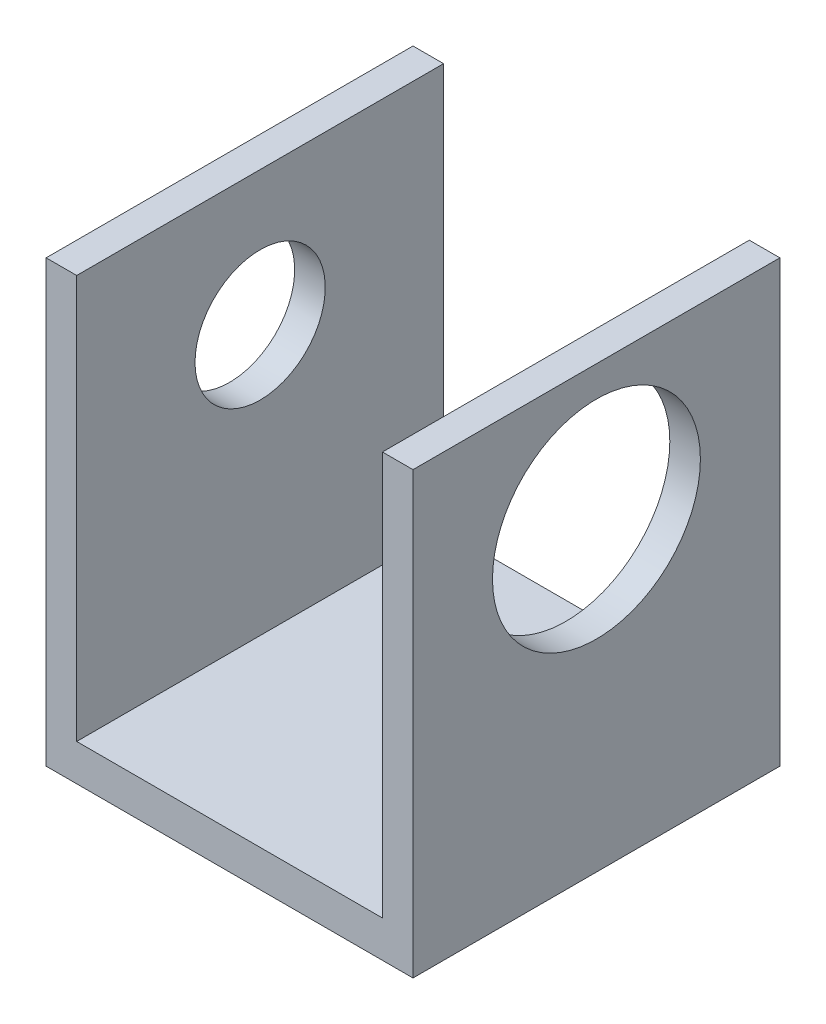
SolidWorks part; units mm, degrees
ref_plane "Front Plane" through (0, 0, 0) normal (0, 0, 1) x (1, 0, 0)
ref_plane "Top Plane" through (0, 0, 0) normal (0, 1, 0) x (1, 0, 0)
ref_plane "Right Plane" through (0, 0, 0) normal (1, 0, 0) x (0, 0, -1)
sketch "Sketch1" plane through (0, 0, 0) normal (0, 0, 1) x (1, 0, 0)
  line L0 (-3.3539, 6.8522) -> (-3.3539, -2.2918)
  line L1 (-3.3539, -2.2918) -> (4.2661, -2.2918)
  line L2 (4.2661, -2.2918) -> (4.2661, 6.8522)
  line L3 (3.6311, 6.8522) -> (3.6311, -1.5298)
  line L4 (3.6311, -1.5298) -> (-2.7189, -1.5298)
  line L5 (-2.7189, -1.5298) -> (-2.7189, 6.8522)
  line L6 (-2.7189, 6.8522) -> (-3.3539, 6.8522)
  line L7 (3.6311, 6.8522) -> (4.2661, 6.8522)
  dimension "D1" = 6.35
  dimension "D2" = 7.62
  dimension "D3" = 0.635
  dimension "D4" = 8.382
  dimension "D5" = 9.144
  dimension "D6" = 8.382
extrude "Boss-Extrude1" add sketch "Sketch1" along normal blind 7.62
sketch "Sketch2" plane through (-3.3539, 0, 0) normal (-1, 0, 0) x (0, 0, 1)
  line L0 (7.62, 6.8522) -> (0, 6.8522) construction
  line L1 (3.81, -2.2918) -> (3.81, 6.8522) construction
  point P0 (3.81, 4.0582)
  dimension "D1" = 2.794
hole_wizard "#6-32 Tapped Hole1" positions "Sketch3" profile "Sketch4" tap size "#6-32" standard "ANSI Inch" end condition up to next
sketch "Sketch3" plane through (-3.3539, 0, 0) normal (-1, 0, 0) x (0, 0, 1)
  point P0 (3.81, 4.0582)
sketch "Sketch4" plane through (-3.3539, 4.0582, 3.81) normal (0, 1, 0) x (0, 0, 1)
  line L0 (0, 0) -> (0, 0.635)
  line L1 (0, 0.635) -> (1.3525, 0.635)
  line L2 (1.3525, 0.635) -> (1.3525, 0)
  line L5 (1.3525, 0) -> (0, 0)
  line L11 (0, -6.35) -> (0, 107.95) construction
  dimension "Thread Major Dia." = 2.7051
  dimension "Thru Tap Drill Depth" = 0.635
sketch "Sketch5" plane through (4.2661, 0, 0) normal (1, 0, 0) x (0, 0, -1)
  point P0 (-3.81, 4.0582)
sketch "Sketch6" plane through (4.2661, 0, 0) normal (1, 0, 0) x (0, 0, -1)
  circle A0 centre (-3.81, 4.0582) radius 2.159
extrude "Cut-Extrude1" cut sketch "Sketch6" against normal up to next
sketch "Sketch12" plane through (-3.3539, 0, 0) normal (-1, 0, 0) x (0, 0, 1)
  line L0 (3.81, -2.2918) -> (3.81, 6.8522) construction
  line L1 (7.62, -2.2918) -> (0, -2.2918) construction
  line L2 (7.62, 6.8522) -> (0, 6.8522) construction
ref_plane "Plane1" through (0.508, 0, 0) normal (1, 0, 0) x (0, 0, -1)
ref_plane "Plane2" through (0, 0, 3.81) normal (0, 0, -1) x (-1, 0, 0)
